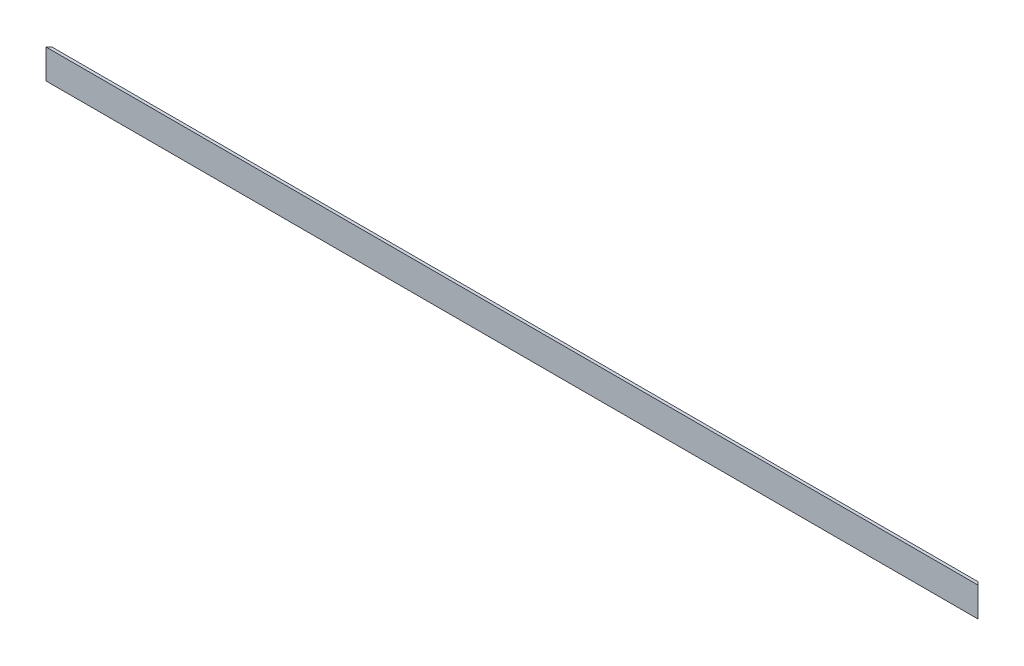
SolidWorks part; units mm, degrees
ref_plane "Спереди" through (0, 0, 0) normal (0, 0, 1) x (1, 0, 0)
ref_plane "Сверху" through (0, 0, 0) normal (0, 1, 0) x (1, 0, 0)
ref_plane "Справа" through (0, 0, 0) normal (1, 0, 0) x (0, 0, -1)
sketch "Эскиз1" plane through (0, 0, 0) normal (1, 0, 0) x (0, 0, -1)
  line L0 (0, 0) -> (0, 15)
  line L1 (0, 15) -> (1.5, 15)
  line L2 (1.5, 15) -> (1.5, 1.5)
  line L3 (1.5, 1.5) -> (15, 1.5)
  line L4 (15, 1.5) -> (15, 0)
  line L5 (15, 0) -> (0, 0)
  dimension "D1" = 15
  dimension "D2" = 15
  dimension "D3" = 1.5
  dimension "D4" = 1.5
extrude "Бобышка-Вытянуть1" add sketch "Эскиз1" along normal blind 475
ref_plane "Плоскость1" through (237.5, 0, 0) normal (1, 0, 0) x (0, 0, -1)
sketch "Эскиз2" plane through (0, 0, 0) normal (0, -1, 0) x (1, 0, 0)
  line L3 (475, 0) -> (454.952, -20.048)
  line L4 (454.952, -20.048) -> (475, -20.048)
  line L5 (475, -20.048) -> (475, 0)
  dimension "D1" = 45
extrude "Вырез-Вытянуть1" cut sketch "Эскиз2" against normal through all
mirror "Зеркальное отражение1" about plane through (237.5, 0, 0) normal (1, 0, 0) of "Вырез-Вытянуть1"
